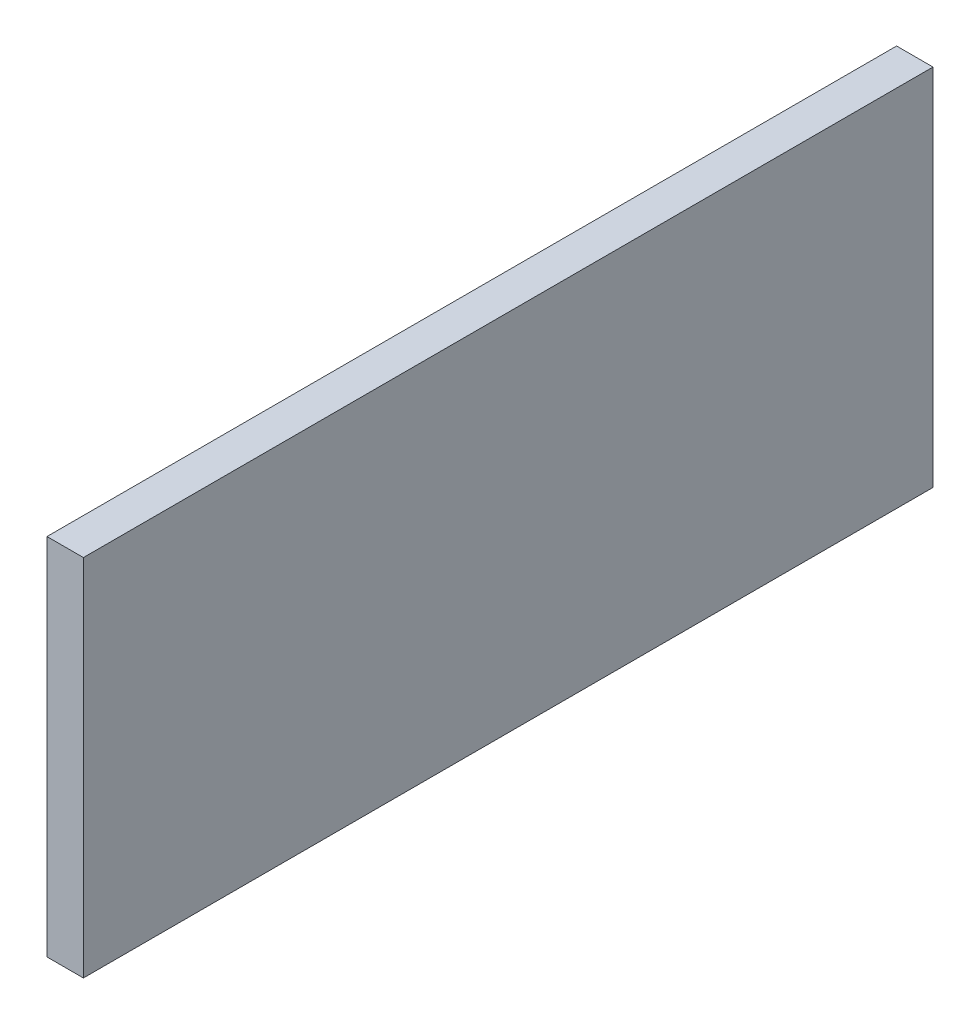
SolidWorks part; units mm, degrees
ref_plane "Front Plane" through (0, 0, 0) normal (0, 0, 1) x (1, 0, 0)
ref_plane "Top Plane" through (0, 0, 0) normal (0, 1, 0) x (1, 0, 0)
ref_plane "Right Plane" through (0, 0, 0) normal (1, 0, 0) x (0, 0, -1)
sketch "Sketch1" plane through (0, 0, 0) normal (1, 0, 0) x (0, 0, -1)
  line L1 (35, -15) -> (-35, -15)
  line L2 (35, -15) -> (35, 15)
  line L3 (35, 15) -> (-35, 15)
  line L4 (-35, -15) -> (-35, 15)
  line L5 (35, -15) -> (-35, 15) construction
  line L6 (35, 15) -> (-35, -15) construction
  point P0 (0, 0)
  dimension "D1" = 30
  dimension "D2" = 70
extrude "Boss-Extrude1" add sketch "Sketch1" along normal blind 3
sketch "Sketch2" plane through (3, 0, 0) normal (1, 0, 0) x (0, 0, -1)
  circle A0 centre (0, 24.7979) radius 30.338
